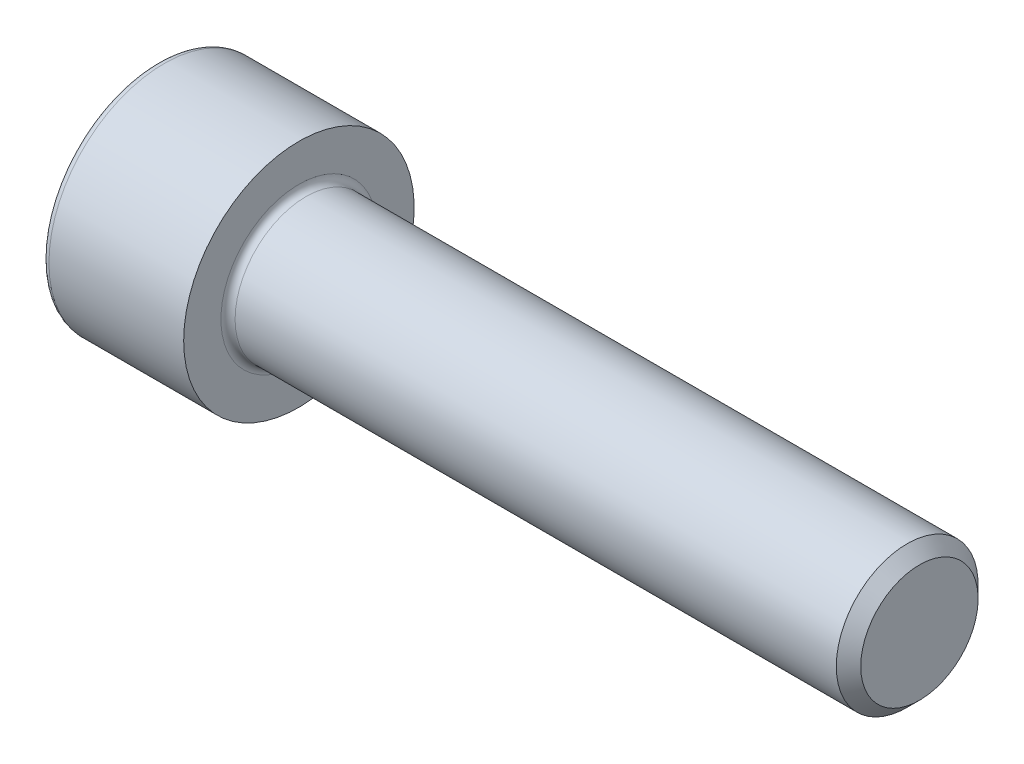
SolidWorks part; units mm, degrees
revolve "Base-Revolve" add sketch "BodySke"
sketch "BodySke" plane through (0, 0, 0) normal (0, 0, 1) x (1, 0, 0)
  line L0 (0, 0) -> (0, 6.5)
  line L1 (0, 6.5) -> (8, 6.5)
  line L2 (8, 6.5) -> (8, 4)
  line L3 (8, 4) -> (42.3095, 4)
  line L4 (43, 3.3095) -> (43, 0)
  line L5 (43, 0) -> (0, 0)
  line L6 (-31.75, 0) -> (127, 0) construction
  line L8 (43, 3.3095) -> (42.3095, 4)
  line L10 (43, -3.3095) -> (42.3095, -4) construction
  line L11 (9.25, 9.525) -> (9.25, 3.175) construction
  line L12 (8, 9.525) -> (8, 3.175) construction
  line L13 (-17, 9.525) -> (-17, 3.175) construction
  dimension "Head_ht" = 8
  dimension "Body_ch_ang" = 45
  dimension "Diameter" = 8
  dimension "Minor_dia" = 6.619
  dimension "Advance" = 1.25
  dimension "Thread_length" = 60
  dimension "Head_dia" = 13
cosmetic thread "ThreadCosmetic" [suppressed]
fillet "Fillet1" radius 0.4 1 edges at (8, 0, 4)
fillet "Fillet2" radius 0.4 1 edges at (0, 0, 6.5)
ref_plane "Plane1" through (0, 0, 0) normal (0, 0, 1) x (1, 0, 0)
ref_plane "Plane2" through (0, 0, 0) normal (0, 1, 0) x (1, 0, 0)
ref_plane "Plane3" through (0, 0, 0) normal (1, 0, 0) x (0, 0, -1)
sketch "Sketch2" plane through (0, 0, 0) normal (0, 0, 1) x (1, 0, 0)
  line L0 (0, 3.0475) -> (4, 3.0475)
  line L1 (4, 3.0475) -> (5.7595, 0)
  line L2 (-31.75, 0) -> (127, 0) construction
  line L3 (5.7595, 0) -> (0, 0)
  line L4 (0, 0) -> (0, 3.0475)
  line L6 (0, 0) -> (47.625, 0) construction
  dimension "D1" = 3.0475
  dimension "D2" = 60
  dimension "Depth" = 4
revolve "Hex-PreBroach" cut sketch "Sketch2" angle 360 about L6
sketch "Sketch3" plane through (0, 0, 0) normal (-1, 0, 0) x (0, 0.5, 0.866)
  line L0 (1.7595, 3.0475) -> (-1.7595, 3.0475)
  line L1 (-1.7595, 3.0475) -> (-3.5189, 0)
  line L2 (1.7595, 3.0475) -> (3.5189, 0)
  line L3 (1.7595, -3.0475) -> (3.5189, 0)
  line L4 (1.7595, -3.0475) -> (-1.7595, -3.0475)
  line L5 (-1.7595, -3.0475) -> (-3.5189, 0)
  dimension "D1" = 3.0475
  dimension "D2" = 3.0475
  dimension "Hex_size" = 6.095
extrude "Hex" cut sketch "Sketch3" against normal blind 4
sketch "ThdSchSke" plane through (0, 0, 0) normal (0, 0, 1) x (1, 0, 0)
  line L0 (11.75, -3.3095) -> (11.2665, -4)
  line L1 (11.75, -3.3095) -> (12.2335, -4)
  line L2 (12.2335, -4) -> (12.2335, -5)
  line L3 (-3.175, 0) -> (5.1513, 0) construction
  line L4 (0, 6.1) -> (0, -6.1) construction
  line L5 (12.2335, -5) -> (11.2665, -5)
  line L6 (11.2665, -5) -> (11.2665, -4)
  dimension "Thread_minor" = 6.619
  dimension "Diameter" = 8
  dimension "Start" = 11.75
revolve "ThreadSchematic" [suppressed] cut sketch "ThdSchSke" angle 360 about L3
pattern_linear "ThdSchPat" [suppressed]
equation "\"D2@Sketch3\" = \"Hex_size@Sketch3\" / 2"
equation "\"D1@Sketch3\" = \"Hex_size@Sketch3\" / 2"
equation "\"D1@Sketch2\" = \"Hex_size@Sketch3\" / 2"
equation "\"Thread_minor@ThreadCosmetic\"  =  \"Minor_dia@BodySke\""
equation "\"Depth@Sketch2\" =  \"Key_eng@Hex\""
equation "\"Thread_length@ThreadCosmetic\" = ((sgn( (\"Length@BodySke\" - \"Advance@BodySke\" * 3.0) - \"Thread_nom@BodySke\" )-1)*( (\"Length@BodySke\" - \"Advance@BodySke\" * 3.0) - \"Thread_nom@BodySke\" ))/-2+ \"Thread_nom@BodySke\""
equation "\"Thread_minor@ThdSchSke\" = \"Minor_dia@BodySke\""
equation "\"Diameter@ThdSchSke\" = \"Diameter@BodySke\""
equation "\"Overcut@ThdSchSke\" = \"Diameter@BodySke\" * 1.25"
equation "\"Start@ThdSchSke\" = \"Head_ht@BodySke\" + \"Length@BodySke\" - \"Thread_length@ThreadCosmetic\"  '---Non-countersunk---"
equation "\"Num_threads@ThdSchPat\" = int( \"Thread_length@ThreadCosmetic\" / \"Advance@BodySke\" + 0.999 )  + 1"
equation "\"Advance@ThdSchPat\" = \"Thread_length@ThreadCosmetic\" /  (\"Num_threads@ThdSchPat\" - 1) 'relax it"
equation "\"Num_threads@ThdSchPat\" = \"Num_threads@ThdSchPat\" - sgn( \"Num_threads@ThdSchPat\" - 1) '---chamfered tips only---"
